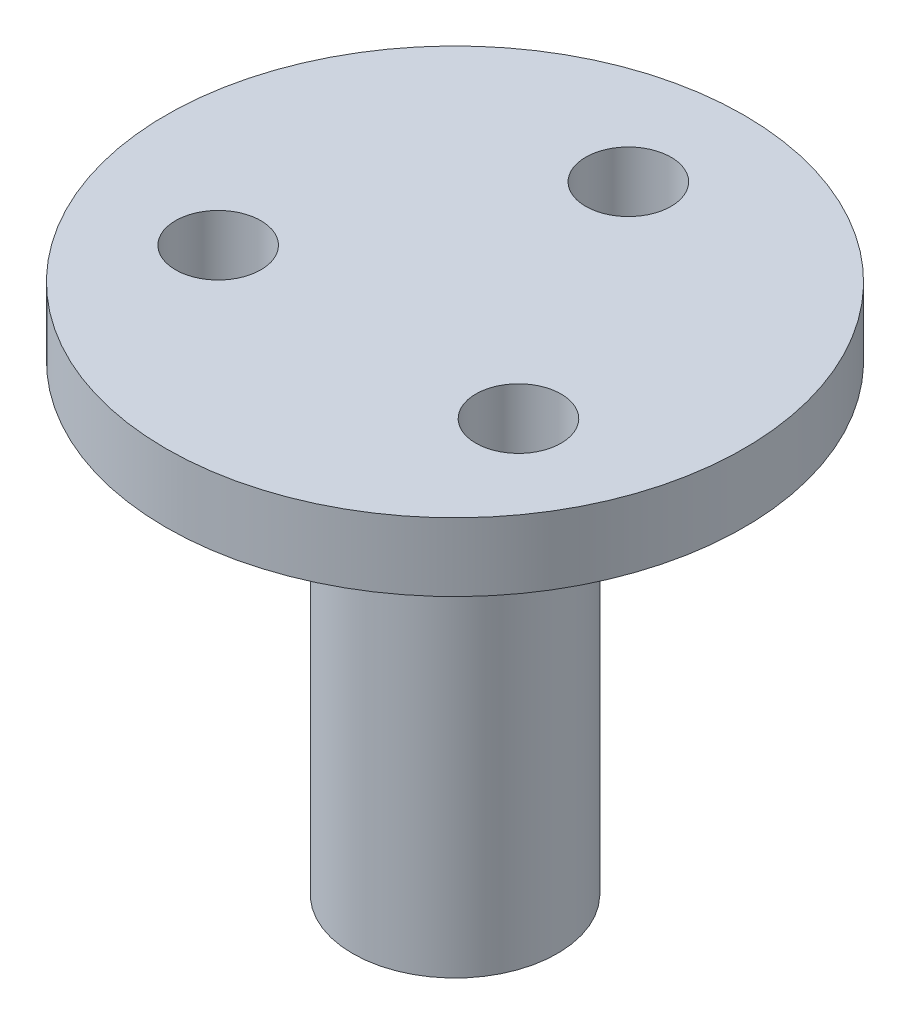
SolidWorks part; units mm, degrees
ref_plane "Front Plane" through (0, 0, 0) normal (0, 0, 1) x (1, 0, 0)
ref_plane "Top Plane" through (0, 0, 0) normal (0, 1, 0) x (1, 0, 0)
ref_plane "Right Plane" through (0, 0, 0) normal (1, 0, 0) x (0, 0, -1)
sketch "Sketch1" plane through (0, 0, 0) normal (0, 1, 0) x (1, 0, 0)
  circle A0 centre (0, 0) radius 4.5
  dimension "D1" = 9
extrude "Boss-Extrude1" add sketch "Sketch1" along normal blind 20.32
sketch "Sketch2" plane through (0, 20.32, 0) normal (0, 1, 0) x (1, 0, 0)
  circle A0 centre (0, 0) radius 12.7
  circle A1 centre (0, 7.62) radius 1.875
  circle A2 centre (6.5991, -3.81) radius 1.875
  circle A3 centre (-6.5991, -3.81) radius 1.875
  point P11 (0, 0)
  dimension "D1" = 3.75
  dimension "D4" = 25.4
  dimension "D2" = 7.62
  dimension "D3" = 3
extrude "Boss-Extrude2" add sketch "Sketch2" along normal blind 3
sketch "Sketch3" plane through (0, 0, 0) normal (0, -1, 0) x (1, 0, 0)
  line L0 (1.4605, 2.0781) -> (1.4605, -2.0781)
  line L1 (0, 0) -> (0, 3.7172) construction
  line L2 (-1.4605, 2.0781) -> (-1.4605, -2.0781)
  arc A0 (-1.4605, -2.0781) -> (1.4605, -2.0781) centre (0, 0) ccw
  arc A1 (1.4605, 2.0781) -> (-1.4605, 2.0781) centre (0, 0) ccw
  dimension "D1" = 5.08
  dimension "D2" = 1.4605
extrude "Cut-Extrude1" cut sketch "Sketch3" against normal blind 5.842
equation "\"D2@Sketch3\"=.115/2"
